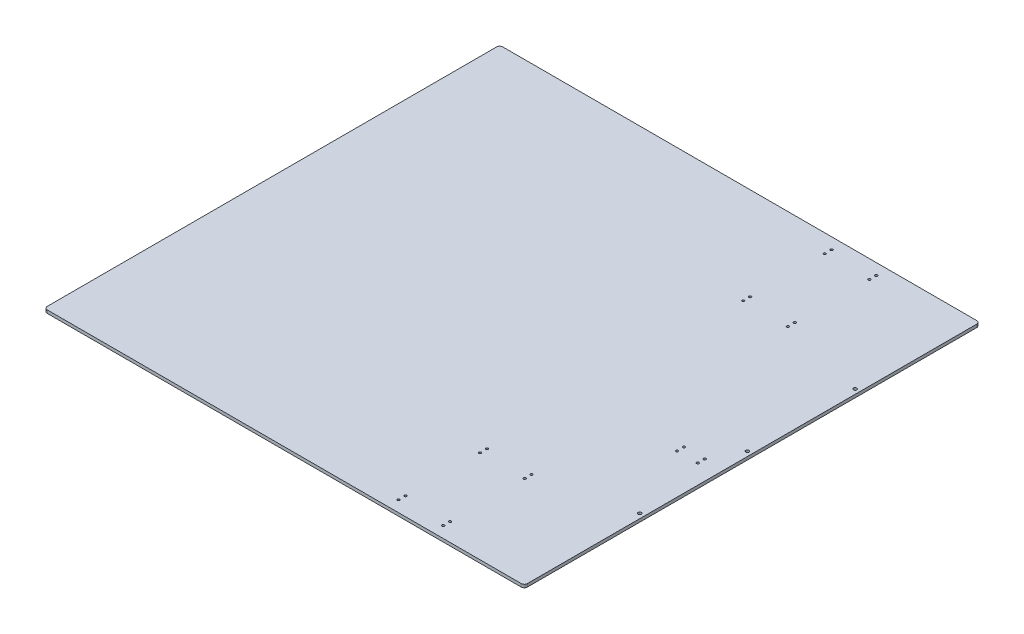
SolidWorks part; units mm, degrees
material "PC High Viscosity"
ref_plane "Front Plane" through (0, 0, 0) normal (0, 0, 1) x (1, 0, 0)
ref_plane "Top Plane" through (0, 0, 0) normal (0, 1, 0) x (1, 0, 0)
ref_plane "Right Plane" through (0, 0, 0) normal (1, 0, 0) x (0, 0, -1)
sketch "Sketch1" plane through (0, 0, 0) normal (0, 0, 1) x (1, 0, 0)
  line L5 (0, 0) -> (0, 6.35)
  line L6 (0, 0) -> (990.6, 0)
  line L7 (0, 6.35) -> (990.6, 6.35)
  line L8 (990.6, 0) -> (990.6, 6.35)
  dimension "D4" = 6.35
  dimension "D5" = 990.6
extrude "Boss-Extrude1" add sketch "Sketch1" along normal mid plane 939.8
sketch "Sketch2" plane through (0, 6.35, 0) normal (0, 1, 0) x (1, 0, 0)
  line L0 (990.6, -469.9) -> (0, -469.9) construction
  line L1 (990.6, -469.9) -> (990.6, 469.9) construction
  circle A0 centre (908.05, -72.263) radius 2.4638
  circle A1 centre (908.05, -58.039) radius 2.4638
  circle A2 centre (950.976, -72.263) radius 2.4638
  circle A3 centre (950.976, -58.039) radius 2.4638
  dimension "D1" = 411.861
  dimension "D4" = 4.9276
  dimension "D2" = 39.624
  dimension "D3" = 82.55
  dimension "D5" = 14.224
extrude "Cut-Extrude1" cut sketch "Sketch2" against normal through all
sketch "Sketch3" plane through (0, 6.35, 0) normal (0, 1, 0) x (1, 0, 0)
  line L0 (990.6, -469.9) -> (0, -469.9) construction
  line L1 (990.6, -469.9) -> (990.6, 469.9) construction
  circle A0 centre (800.1, -446.786) radius 2.4638
  circle A1 centre (708.025, -446.786) radius 2.4638
  circle A2 centre (708.025, -432.562) radius 2.4638
  circle A3 centre (800.1, -432.562) radius 2.4638
  circle A4 centre (708.025, -264.414) radius 2.4638
  circle A5 centre (708.025, -278.638) radius 2.4638
  circle A6 centre (800.1, -264.414) radius 2.4638
  circle A7 centre (800.1, -278.638) radius 2.4638
  dimension "D1" = 23.114
  dimension "D5" = 4.9276
  dimension "D2" = 14.224
  dimension "D3" = 14.224
  dimension "D4" = 205.486
  dimension "D6" = 190.5
  dimension "D7" = 282.575
extrude "Cut-Extrude2" cut sketch "Sketch3" against normal through all
mirror "Mirror1" about plane through (0, 0, 0) normal (0, 0, 1) of "Cut-Extrude2"
sketch "Sketch4" plane through (0, 6.35, 0) normal (0, 1, 0) x (1, 0, 0)
  line L0 (990.6, -469.9) -> (990.6, 469.9) construction
  circle A0 centre (981.075, 0) radius 3.3655
  circle A1 centre (981.075, 222.25) radius 3.3655
  circle A2 centre (981.075, -222.25) radius 3.3655
  dimension "D1" = 9.525
  dimension "D2" = 6.731
  dimension "D5" = 222.25
  dimension "D6" = 222.25
  dimension "D3" = 2
  dimension "D4" = 2
extrude "Cut-Extrude3" cut sketch "Sketch4" against normal through all
fillet "Fillet1" radius 6.35 4 edges at (0, 3.175, -469.9) (990.6, 3.175, -469.9) (990.6, 3.175, 469.9) (0, 3.175, 469.9)
